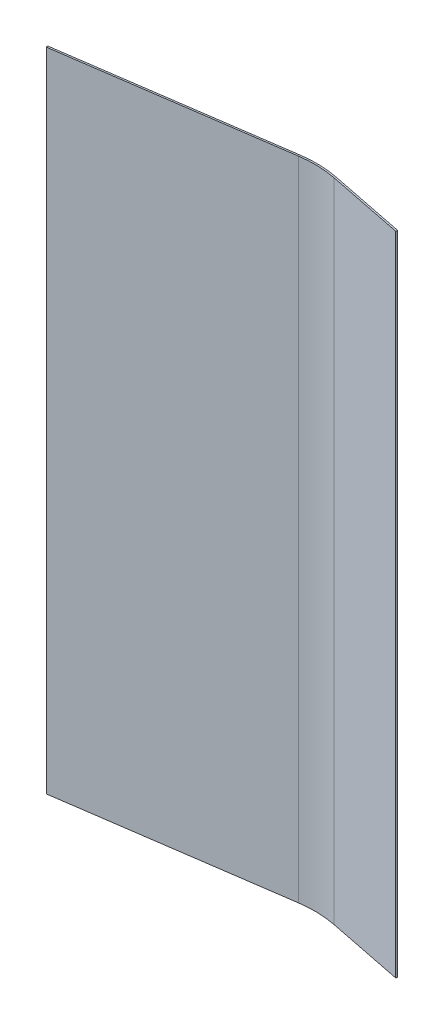
SolidWorks part; units mm, degrees
material "Acrylic (Medium-high impact)"
ref_plane "Front Plane" through (0, 0, 0) normal (0, 0, 1) x (1, 0, 0)
ref_plane "Top Plane" through (0, 0, 0) normal (0, 1, 0) x (1, 0, 0)
ref_plane "Right Plane" through (0, 0, 0) normal (1, 0, 0) x (0, 0, -1)
sketch "Sketch1" plane through (0, 0, 0) normal (0, 1, 0) x (1, 0, 0)
  line L0 (0, 0) -> (225.0917, 32.3921)
  line L1 (225.0917, 32.3921) -> (314.9558, 14.4355)
  line L2 (0, 0) -> (266.6925, 0) construction
  line L3 (-0.2261, 1.5713) -> (225.1354, 34.0022)
  line L4 (225.1354, 34.0022) -> (315.2669, 15.9922)
  line L5 (-0.2261, 1.5713) -> (0, 0)
  line L6 (315.2669, 15.9922) -> (314.9558, 14.4355)
  dimension "D1" = 8.189
  dimension "D2" = 91.6407
  dimension "D3" = 227.6831
  dimension "D4" = 11.3
  dimension "D5" = 1.5875
extrude "ForCAD" add sketch "Sketch1" along normal blind 609.6
sketch "ForShop" plane through (0, 0, 0) normal (0, 0, 1) x (1, 0, 0)
  line L0 (0, 0) -> (225.0917, 0) construction
  line L1 (-0.2261, 609.6) -> (319.8139, 609.6)
  line L2 (-0.2261, 609.6) -> (-0.2261, 0)
  line L3 (-0.2261, 0) -> (319.8139, 0)
  line L4 (319.8139, 609.6) -> (319.8139, 0)
  line L5 (319.8139, 609.6) -> (228.3739, 609.6) construction
  line L6 (228.3739, 609.6) -> (228.3739, 0) construction
  dimension "D1" = 320.04
  dimension "D2" = 91.44
fillet "Fillet1" radius 101.6 2 edges at (225.0917, 304.8, -32.3921) (225.1354, 304.8, -34.0022)
